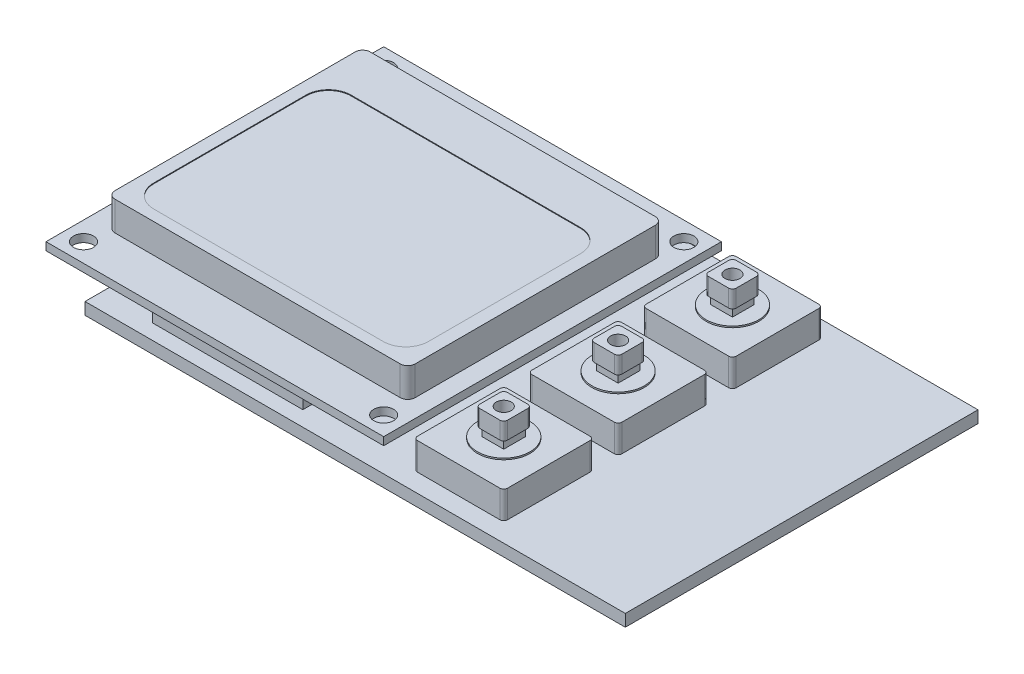
SolidWorks part; units mm, degrees
ref_plane "Front Plane" through (0, 0, 0) normal (0, 0, 1) x (1, 0, 0)
ref_plane "Top Plane" through (0, 0, 0) normal (0, 1, 0) x (1, 0, 0)
ref_plane "Right Plane" through (0, 0, 0) normal (1, 0, 0) x (0, 0, -1)
sketch "Sketch1" plane through (0, 0, 0) normal (0, 1, 0) x (1, 0, 0)
  line L1 (-36, 23.5) -> (36, 23.5)
  line L2 (-36, 23.5) -> (-36, -23.5)
  line L3 (-36, -23.5) -> (36, -23.5)
  line L4 (36, 23.5) -> (36, -23.5)
  line L5 (-36, 23.5) -> (36, -23.5) construction
  line L6 (-36, -23.5) -> (36, 23.5) construction
  point P0 (0, 0)
  dimension "D1" = 72
  dimension "D2" = 47
extrude "Boss-Extrude1" add sketch "Sketch1" along normal blind 1.6
sketch "Sketch2" plane through (0, 1.6, 0) normal (0, 1, 0) x (1, 0, 0)
  line L0 (-36, 23.5) -> (-36, -23.5) construction
  line L1 (-29, -21.4751) -> (-9, -21.4751)
  line L2 (-29, -21.4751) -> (-29, -18.4751)
  line L3 (-29, -18.4751) -> (-9, -18.4751)
  line L4 (-9, -21.4751) -> (-9, -18.4751)
  line L5 (-36, 0) -> (36, 0) construction
  line L6 (36, -23.5) -> (36, 23.5) construction
  line L7 (-9, 21.4751) -> (-9, 18.4751)
  line L8 (-29, 18.4751) -> (-9, 18.4751)
  line L9 (-29, 21.4751) -> (-29, 18.4751)
  line L10 (-29, 21.4751) -> (-9, 21.4751)
  dimension "D1" = 7
  dimension "D2" = 20
  dimension "D3" = 3
extrude "Boss-Extrude2" add sketch "Sketch2" along normal blind 2.6
sketch "Sketch3" plane through (0, 4.2, 0) normal (0, 1, 0) x (1, 0, 0)
  line L0 (36, 23.5) -> (-36, 23.5) construction
  line L1 (-41.85, 22.15) -> (3.15, 22.15)
  line L2 (-41.85, 22.15) -> (-41.85, -22.85)
  line L3 (-41.85, -22.85) -> (3.15, -22.85)
  line L4 (3.15, 22.15) -> (3.15, -22.85)
  line L5 (-36, 23.5) -> (-36, -23.5) construction
  line L6 (-19.35, 22.15) -> (-19.35, -22.85) construction
  line L7 (-41.85, -0.35) -> (3.15, -0.35) construction
  circle A0 centre (-39.35, 19.65) radius 1.325
  circle A1 centre (0.65, 19.65) radius 1.325
  circle A2 centre (0.65, -20.35) radius 1.325
  circle A3 centre (-39.35, -20.35) radius 1.325
  dimension "D5" = 2.65
  dimension "D1" = 45
  dimension "D2" = 45
  dimension "D3" = 1.35
  dimension "D4" = 5.85
  dimension "D6" = 2.5
  dimension "D7" = 2.5
extrude "Boss-Extrude3" add sketch "Sketch3" along normal blind 1.05
sketch "Sketch4" plane through (0, 5.25, 0) normal (0, 1, 0) x (1, 0, 0)
  line L0 (3.15, 22.15) -> (-41.85, 22.15) construction
  line L1 (-39.25, 16.75) -> (0.75, 16.75)
  line L2 (-39.25, 16.75) -> (-39.25, -17.25)
  line L3 (-39.25, -17.25) -> (0.75, -17.25)
  line L4 (0.75, 16.75) -> (0.75, -17.25)
  line L5 (-41.85, 22.15) -> (-41.85, -22.85) construction
  dimension "D1" = 40
  dimension "D2" = 34
  dimension "D3" = 5.4
  dimension "D4" = 2.6
extrude "Boss-Extrude4" add sketch "Sketch4" along normal blind 3.9
sketch "Sketch5" plane through (0, 9.15, 0) normal (0, 1, 0) x (1, 0, 0)
  line L0 (-39.25, -17.25) -> (0.75, -17.25) construction
  line L1 (-34.55, -15.8) -> (-3.95, -15.8)
  line L2 (-37.55, -12.8) -> (-37.55, 7.5)
  line L3 (-34.55, 10.5) -> (-3.95, 10.5)
  line L4 (-0.95, -12.8) -> (-0.95, 7.5)
  line L5 (-19.25, 16.75) -> (-19.25, -22.8501) construction
  line L8 (0.75, 16.75) -> (-39.25, 16.75) construction
  line L10 (-19.25, 10.5) -> (-19.25, -15.8) construction
  arc A0 (-3.95, 10.5) -> (-0.95, 7.5) centre (-3.95, 7.5) cw
  arc A1 (-3.95, -15.8) -> (-0.95, -12.8) centre (-3.95, -12.8) ccw
  arc A2 (-34.55, -15.8) -> (-37.55, -12.8) centre (-34.55, -12.8) cw
  arc A3 (-37.55, 7.5) -> (-34.55, 10.5) centre (-34.55, 7.5) cw
  point P16 (-0.95, -15.8)
  point P19 (-37.55, -15.8)
  point P22 (-37.55, 10.5)
  dimension "D4" = 3
  dimension "D1" = 36.6
  dimension "D2" = 26.3
  dimension "D3" = 1.45
extrude "Cut-Extrude1" cut sketch "Sketch5" against normal blind 0.1
fillet "Fillet1" radius 1 4 edges at (-39.25, 7.2, -16.75) (0.75, 7.2, -16.75) (0.75, 7.2, 17.25) (-39.25, 7.2, 17.25)
sketch "Sketch6" plane through (0, 1.6, 0) normal (0, 1, 0) x (1, 0, 0)
  line L0 (-36, -23.5) -> (36, -23.5) construction
  line L1 (5.35, -21.05) -> (17.35, -21.05)
  line L2 (5.35, -21.05) -> (5.35, -9.05)
  line L3 (5.35, -9.05) -> (17.35, -9.05)
  line L4 (17.35, -21.05) -> (17.35, -9.05)
  line L5 (3.15, -22.85) -> (3.15, 22.15) construction
  dimension "D1" = 12
  dimension "D2" = 12
  dimension "D3" = 2.45
  dimension "D4" = 2.2
extrude "Boss-Extrude5" add sketch "Sketch6" along normal blind 3.65
sketch "Sketch7" plane through (0, 5.25, 0) normal (0, 1, 0) x (1, 0, 0)
  line L0 (11.35, -9.05) -> (11.35, -21.05) construction
  line L1 (17.35, -9.05) -> (5.35, -9.05) construction
  line L2 (5.35, -21.05) -> (17.35, -21.05) construction
  line L3 (5.35, -15.05) -> (17.35, -15.05) construction
  line L4 (5.35, -9.05) -> (5.35, -21.05) construction
  line L5 (17.35, -21.05) -> (17.35, -9.05) construction
  circle A0 centre (11.35, -15.05) radius 3.5
  point P12 (11.35, -15.05)
  dimension "D1" = 7
extrude "Boss-Extrude6" add sketch "Sketch7" along normal blind 0.2
sketch "Sketch8" plane through (0, 5.45, 0) normal (0, 1, 0) x (1, 0, 0)
  line L0 (11.35, -11.55) -> (11.35, -18.55) construction
  line L1 (7.85, -15.05) -> (14.85, -15.05) construction
  line L3 (9.9, -13.6) -> (12.8, -13.6)
  line L4 (9.9, -13.6) -> (9.9, -16.5)
  line L5 (9.9, -16.5) -> (12.8, -16.5)
  line L6 (12.8, -13.6) -> (12.8, -16.5)
  line L7 (9.9, -13.6) -> (12.8, -16.5) construction
  line L8 (9.9, -16.5) -> (12.8, -13.6) construction
  circle A0 centre (11.35, -15.05) radius 3.5 construction
  circle A1 centre (11.35, -15.05) radius 3.5 construction
  point P9 (11.35, -15.05)
  dimension "D1" = 2.9
extrude "Boss-Extrude7" add sketch "Sketch8" along normal blind 1.2
sketch "Sketch9" plane through (0, 6.65, 0) normal (0, 1, 0) x (1, 0, 0)
  line L0 (11.35, -13.6) -> (11.35, -16.5) construction
  line L1 (12.8, -13.6) -> (9.9, -13.6) construction
  line L2 (9.9, -16.5) -> (12.8, -16.5) construction
  line L3 (9.9, -15.05) -> (12.8, -15.05) construction
  line L4 (9.9, -13.6) -> (9.9, -16.5) construction
  line L5 (12.8, -16.5) -> (12.8, -13.6) construction
  line L7 (13.2, -13.2) -> (9.5, -13.2)
  line L8 (13.2, -13.2) -> (13.2, -16.9)
  line L9 (13.2, -16.9) -> (9.5, -16.9)
  line L10 (9.5, -13.2) -> (9.5, -16.9)
  line L11 (13.2, -13.2) -> (9.5, -16.9) construction
  line L12 (13.2, -16.9) -> (9.5, -13.2) construction
  point P12 (11.35, -15.05)
  dimension "D1" = 3.7
extrude "Boss-Extrude8" add sketch "Sketch9" along normal blind 2.3
fillet "Fillet2" radius 0.5 8 edges at (9.5, 7.8, 13.2) (13.2, 7.8, 13.2) (17.35, 3.425, 9.05) (5.35, 3.425, 9.05) (13.2, 7.8, 16.9) (9.5, 7.8, 16.9) (17.35, 3.425, 21.05) (5.35, 3.425, 21.05)
sketch "Sketch10" plane through (0, 8.95, 0) normal (0, 1, 0) x (1, 0, 0)
  line L0 (11.35, -13.2) -> (11.35, -16.9) construction
  line L1 (12.7, -13.2) -> (10, -13.2) construction
  line L2 (10, -16.9) -> (12.7, -16.9) construction
  line L3 (9.5, -15.05) -> (13.2, -15.05) construction
  line L4 (9.5, -13.7) -> (9.5, -16.4) construction
  line L5 (13.2, -16.4) -> (13.2, -13.7) construction
  circle A0 centre (11.35, -15.05) radius 1
  dimension "D1" = 2
extrude "Cut-Extrude2" cut sketch "Sketch10" against normal blind 3
pattern_linear "LPattern1" count 3 spacing 15.24 along (0, 0, -1) of "Boss-Extrude5", "Boss-Extrude6", "Boss-Extrude8", "Boss-Extrude7", "Fillet2", "Cut-Extrude2"
